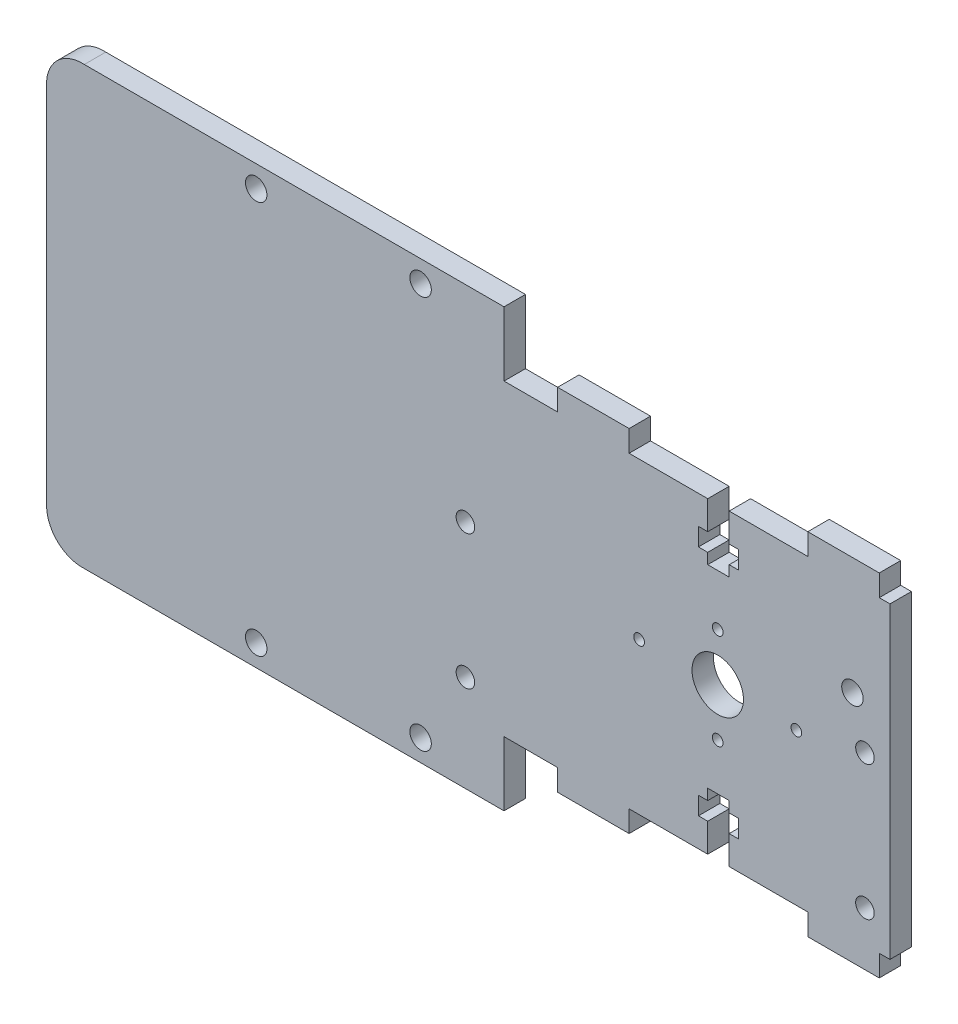
SolidWorks part; units mm, degrees
ref_plane "Front Plane" through (0, 0, 0) normal (0, 0, 1) x (1, 0, 0)
ref_plane "Top Plane" through (0, 0, 0) normal (0, 1, 0) x (1, 0, 0)
ref_plane "Right Plane" through (0, 0, 0) normal (1, 0, 0) x (0, 0, -1)
sketch "Model" plane through (0, 0, 0) normal (0, 0, 1) x (1, 0, 0)
  line L1 (88.808, 39.598) -> (4.308, 39.598) construction
  line L4 (43.808, 64.448) -> (43.808, 61.448)
  line L6 (43.808, 15.368) -> (43.808, 18.368)
  line L7 (53.808, 15.368) -> (43.808, 15.368)
  line L8 (53.808, 18.368) -> (53.808, 15.368)
  line L9 (64.808, 18.368) -> (53.808, 18.368)
  line L10 (64.808, 22.368) -> (64.808, 18.368)
  line L11 (63.508, 22.368) -> (64.808, 22.368)
  line L12 (63.508, 24.868) -> (63.508, 22.368)
  line L13 (64.808, 24.868) -> (63.508, 24.868)
  line L14 (64.808, 26.368) -> (64.808, 24.868)
  line L15 (67.808, 26.368) -> (64.808, 26.368)
  line L16 (67.808, 24.868) -> (67.808, 26.368)
  line L17 (69.108, 24.868) -> (67.808, 24.868)
  line L18 (69.108, 22.368) -> (69.108, 24.868)
  line L19 (67.808, 22.368) -> (69.108, 22.368)
  line L20 (67.808, 18.368) -> (67.808, 22.368)
  line L21 (78.808, 18.368) -> (67.808, 18.368)
  line L22 (78.808, 15.368) -> (78.808, 18.368)
  line L23 (88.808, 15.368) -> (78.808, 15.368)
  line L24 (78.808, 64.448) -> (88.808, 64.448)
  line L25 (78.808, 61.448) -> (78.808, 64.448)
  line L26 (67.808, 61.448) -> (78.808, 61.448)
  line L27 (67.808, 57.4481) -> (67.808, 61.448)
  line L28 (69.108, 57.4481) -> (67.808, 57.4481)
  line L29 (69.108, 54.9481) -> (69.108, 57.4481)
  line L30 (67.808, 54.9481) -> (69.108, 54.9481)
  line L31 (67.808, 53.448) -> (67.808, 54.9481)
  line L32 (64.808, 53.448) -> (67.808, 53.448)
  line L33 (64.808, 54.9481) -> (64.808, 53.448)
  line L34 (63.508, 54.9481) -> (64.808, 54.9481)
  line L35 (63.508, 57.4481) -> (63.508, 54.9481)
  line L36 (64.808, 57.4481) -> (63.508, 57.4481)
  line L37 (64.808, 61.448) -> (64.808, 57.4481)
  line L38 (53.808, 61.448) -> (64.808, 61.448)
  line L39 (53.808, 64.448) -> (53.808, 61.448)
  line L40 (43.808, 64.448) -> (53.808, 64.448)
  line L41 (42.558, 48.068) -> (85.058, 48.068) construction
  line L42 (1.308, 39.6674) -> (55.2079, 39.5877) construction
  line L44 (88.808, 61.448) -> (90.308, 61.448)
  line L45 (90.308, 61.448) -> (90.308, 18.368)
  line L46 (90.308, 18.368) -> (88.808, 18.368)
  line L47 (88.808, 64.448) -> (88.808, 61.448)
  line L48 (88.808, 18.368) -> (88.808, 15.368)
  line L49 (30.908, 41.668) -> (86.808, 41.668) construction
  line L50 (30.908, 41.668) -> (30.908, 22.868) construction
  line L51 (30.908, 22.868) -> (86.808, 22.868) construction
  line L52 (66.208, 46.298) -> (66.208, 39.598) construction
  line L53 (36.308, 61.448) -> (36.308, 70.448)
  line L54 (36.308, 70.448) -> (-22.4142, 70.448)
  line L55 (36.308, 18.368) -> (36.308, 9.368)
  line L56 (36.308, 9.368) -> (-22.4142, 9.368)
  line L57 (43.808, 61.448) -> (36.308, 61.448)
  line L58 (43.808, 18.368) -> (36.308, 18.368)
  line L59 (-27.6928, 14.3602) -> (-27.6928, 65.743)
  line L60 (1.6358, 67.408) -> (24.6358, 67.408) construction
  line L61 (1.6358, 67.408) -> (1.6358, 12.408) construction
  line L62 (1.6358, 12.408) -> (24.6358, 12.408) construction
  line L63 (24.6358, 12.408) -> (24.6358, 67.408) construction
  circle A0 centre (66.208, 39.598) radius 3.6
  circle A1 centre (66.208, 39.598) radius 3.6
  circle A2 centre (55.2079, 39.5877) radius 0.75
  circle A3 centre (66.208, 46.298) radius 0.75
  circle A4 centre (66.208, 32.898) radius 0.75
  circle A5 centre (77.208, 39.598) radius 0.75
  circle A7 centre (85.058, 48.068) radius 1.5
  arc A8 (-22.4142, 70.448) -> (-27.6928, 65.743) centre (-22.701, 65.4562) ccw
  arc A9 (-27.6928, 14.3602) -> (-22.4142, 9.368) centre (-22.6928, 14.3602) ccw
  circle A13 centre (30.908, 41.668) radius 1.3
  circle A14 centre (86.808, 41.668) radius 1.3
  circle A15 centre (30.908, 22.868) radius 1.3
  circle A16 centre (86.808, 22.868) radius 1.3
  circle A17 centre (1.6358, 67.408) radius 1.5
  circle A18 centre (24.6358, 67.408) radius 1.5
  circle A19 centre (1.6358, 12.408) radius 1.5
  circle A20 centre (24.6358, 12.408) radius 1.5
  point P12 (0, 0)
  dimension "D8" = 3
  dimension "D18" = 5.25
  dimension "D21" = 55.9
  dimension "D22" = 18.8
  dimension "D23" = 55.9
  dimension "D24" = 3.5
  dimension "D25" = 4.5
  dimension "D26" = 6.7
  dimension "D28" = 11.0001
  dimension "D29" = 11
  dimension "D33" = 23
  dimension "D35" = 3.04
  dimension "D1" = 3
  dimension "D2" = 10
  dimension "D3" = 3.9999
  dimension "D4" = 1.5
  dimension "D9" = 8
  dimension "D10" = 4
  dimension "D11" = 2.5
  dimension "D12" = 3
  dimension "D13" = 1.3
  dimension "D14" = 11
  dimension "D15" = 1.3
  dimension "D16" = 11
  dimension "D17" = 10
  dimension "D19" = 3
  dimension "D20" = 3
  dimension "D27" = 6.7
  dimension "D30" = 10
  dimension "D31" = 9
  dimension "D32" = 9
  dimension "D34" = 55
  dimension "D36" = 7.5
extrude "Boss-Extrude1" add sketch "Model" along normal blind 3
